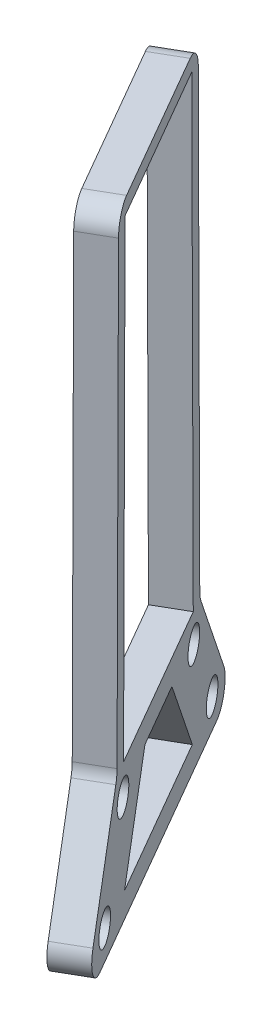
SolidWorks part; units mm, degrees
ref_plane "Front Plane" through (0, 0, 0) normal (0, 0, 1) x (1, 0, 0)
ref_plane "Top Plane" through (0, 0, 0) normal (0, 1, 0) x (1, 0, 0)
ref_plane "Right Plane" through (0, 0, 0) normal (1, 0, 0) x (0, 0, -1)
sketch "Sketch1" plane through (7.8704, 0, -4.544) normal (-0.866, 0, 0.5) x (0.5, 0, 0.866)
  line L4 (28.5771, 200.5668) -> (28.0206, 136.7988)
  line L6 (28.5771, 200.5668) -> (53.2948, 200.5668)
  line L7 (53.2948, 200.5668) -> (53.8513, 136.7988)
  line L9 (28.7753, 200.3668) -> (28.4245, 160.1668) construction
  line L13 (13.7886, 118.0559) -> (25.6059, 136.7988)
  line L14 (25.6059, 136.7988) -> (56.266, 136.7988)
  line L15 (56.266, 136.7988) -> (68.0832, 118.0559)
  line L16 (68.0832, 118.0559) -> (13.7886, 118.0559)
  line L17 (28.3701, 121.4274) -> (35.9359, 133.4274)
  line L18 (35.9359, 133.4274) -> (45.9359, 133.4274)
  line L19 (45.9359, 133.4274) -> (53.5018, 121.4274)
  line L20 (53.5018, 121.4274) -> (28.3701, 121.4274)
  line L26 (34.5859, 200.3668) -> (47.2859, 200.3668) construction
  line L27 (53.4473, 160.1668) -> (53.0965, 200.3668) construction
  line L28 (55.692, 202.5668) -> (56.266, 136.7988)
  line L29 (26.1798, 202.5668) -> (55.692, 202.5668)
  line L30 (26.1798, 202.5668) -> (25.6059, 136.7988)
  circle A4 centre (27.8126, 132.7988) radius 2.15
  circle A5 centre (54.0593, 132.7988) radius 2.15
  circle A6 centre (60.8326, 122.0559) radius 2.15
  circle A7 centre (21.0393, 122.0559) radius 2.15
  point P1 (19.6973, 127.4274)
  point P3 (32.153, 127.4274)
  point P4 (27.8126, 132.7988)
  point P13 (40.9359, 136.7988)
  point P14 (40.9359, 133.4274)
  point P26 (23.3597, 202.5668)
  point P27 (0, 0)
  point P28 (0, 0)
  point P29 (0, 0)
  point P30 (0, 0)
  point P31 (0, 0)
  line M35 (28.2863, 134.8601) -> (28.8129, 135.6288)
  line M36 (28.8129, 135.6288) -> (28.491, 135.8493)
  arc M37 (28.491, 135.8493) -> (27.6103, 135.9173) centre (27.8126, 132.7988) ccw
  line M38 (27.6103, 135.9173) -> (25.51, 134.9116)
  arc M39 (25.51, 134.9116) -> (25.0108, 134.1828) centre (27.8126, 132.7988) ccw
  line M40 (25.0108, 134.1828) -> (24.8316, 131.8611)
  arc M41 (24.8316, 131.8611) -> (25.2131, 131.0644) centre (27.8126, 132.7988) ccw
  line M42 (25.2131, 131.0644) -> (25.535, 130.8439)
  line M43 (25.535, 130.8439) -> (26.0616, 131.6125)
  dimension "D1" = 4.3
  dimension "D2" = 4
  dimension "D3" = 4
  dimension "D4" = 4
  dimension "D5" = 4
  dimension "D6" = 4
  dimension "D7" = 10
  dimension "D8" = 12
  dimension "D9" = 4
  dimension "D10" = 0.2
  dimension "D11" = 0.2
  dimension "D12" = 0.2
  dimension "D13" = 2
extrude "Boss-Extrude1" add sketch "Sketch1" along normal blind 4.45 contours L16 L15 L14 L13 A7 A6 A5 A4 L19 L20 L17 L18 M43 M42 M41 M40 M39 M38 M37 M36 M35 | L29 L30 L14 L4 L6 L7 L28 | A4 M35 M36 M37 M38 M39 M40 M41 M42 M43
fillet "Fillet1" radius 3 6 edges at (33.7895, 202.5668, 44.7992) (19.0334, 202.5668, 19.2409) (18.7464, 136.7988, 18.7439) (34.0765, 136.7988, 45.2963) (39.9851, 118.0559, 55.5303) (12.8378, 118.0559, 8.5098)
